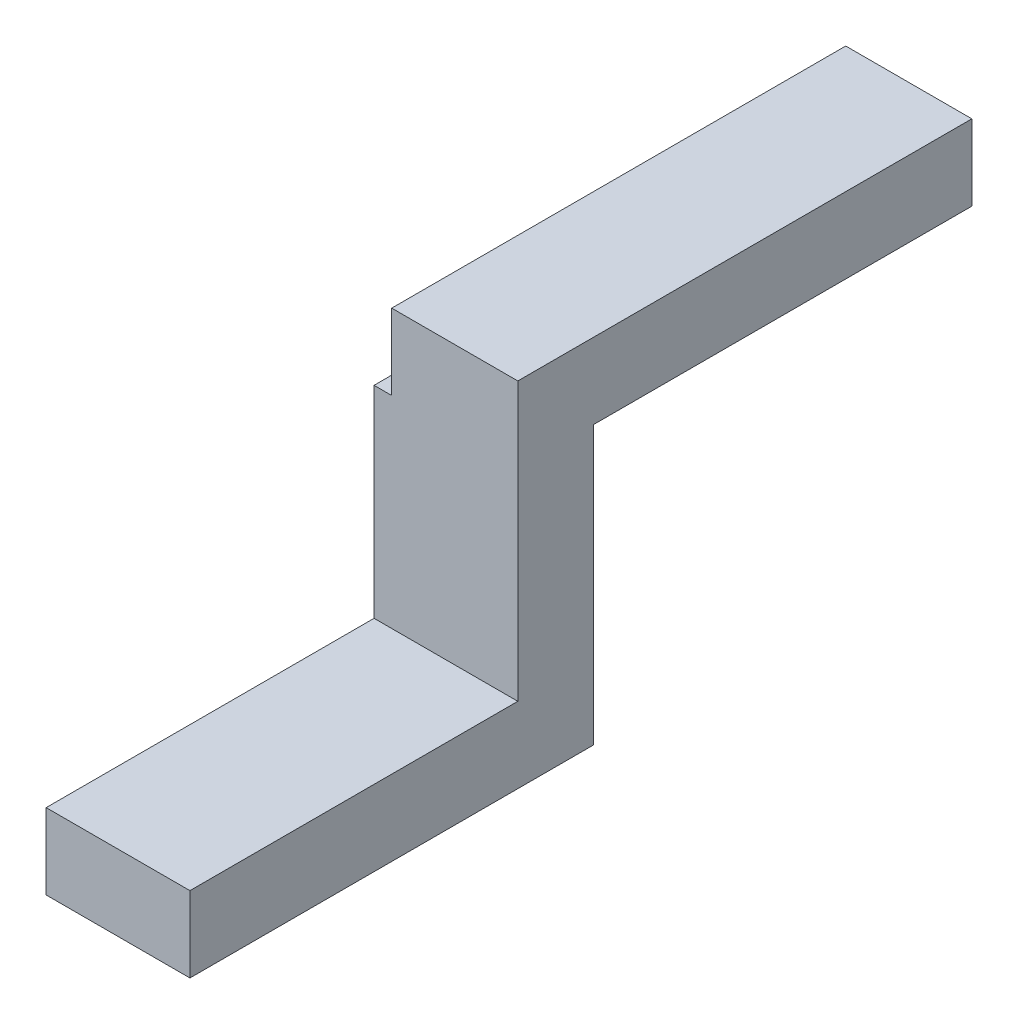
SolidWorks part; units mm, degrees
ref_plane "Front Plane" through (0, 0, 0) normal (0, 0, 1) x (1, 0, 0)
ref_plane "Top Plane" through (0, 0, 0) normal (0, 1, 0) x (1, 0, 0)
ref_plane "Right Plane" through (0, 0, 0) normal (1, 0, 0) x (0, 0, -1)
sketch "Sketch1" plane through (0, 0, 0) normal (1, 0, 0) x (0, 0, -1)
  line L0 (-16, 3) -> (-3, 3)
  line L1 (-3, 3) -> (-3, 14)
  line L2 (-3, 14) -> (15, 14)
  line L3 (15, 14) -> (15, 11)
  line L4 (15, 11) -> (0, 11)
  line L5 (0, 11) -> (0, 0)
  line L6 (0, 0) -> (-16, 0)
  line L7 (-16, 0) -> (-16, 3)
  point P3 (0, -2.0847)
  point P10 (-4.1695, 0)
  point P11 (0, -3.4068)
  point P12 (-4.3729, 3)
  point P13 (0, 0)
  dimension "D1" = 3
  dimension "D2" = 3
  dimension "D3" = 3
  dimension "D4" = 15
  dimension "D5" = 13
  dimension "D6" = 8
extrude "Boss-Extrude1" add sketch "Sketch1" along normal blind 5.7
sketch "Sketch2" plane through (0, 0, 3) normal (0, 0, 1) x (1, 0, 0)
  line L0 (5.7, 14) -> (5.7, 3) construction
  line L1 (0, 14) -> (0.7, 14)
  line L2 (0, 14) -> (0, 11)
  line L3 (0, 11) -> (0.7, 11)
  line L4 (0.7, 14) -> (0.7, 11)
  point P7 (0, 0)
  point P10 (5.4328, 10.6864)
  dimension "D1" = 5
extrude "Cut-Extrude1" cut sketch "Sketch2" against normal through all
